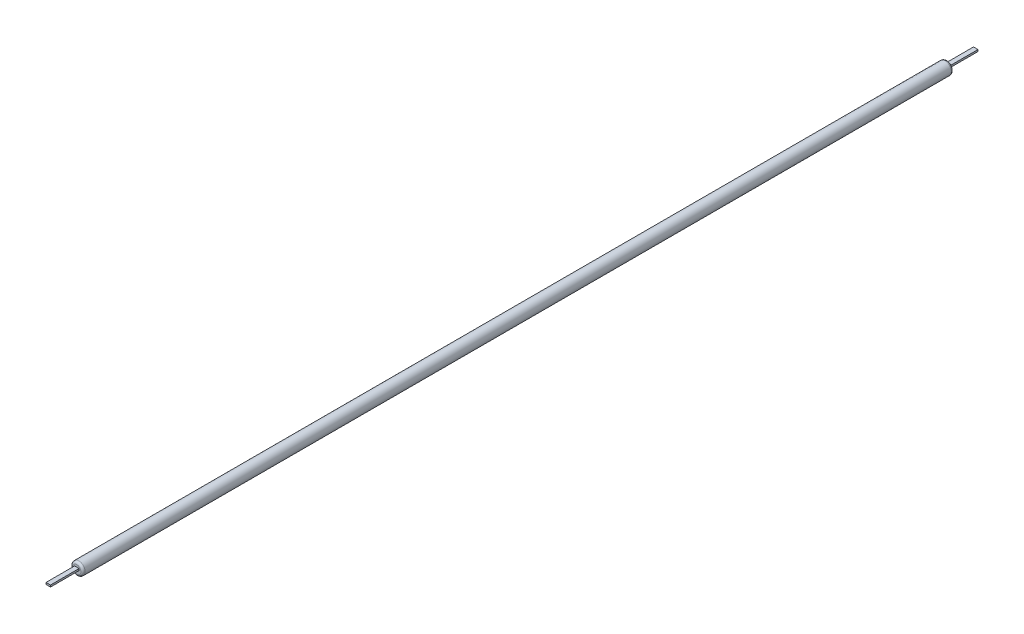
SolidWorks part; units mm, degrees
material "Plastique personnalisé"
ref_plane "Plan de face" through (0, 0, 0) normal (0, 0, 1) x (1, 0, 0)
ref_plane "Plan de dessus" through (0, 0, 0) normal (0, 1, 0) x (1, 0, 0)
ref_plane "Plan de droite" through (0, 0, 0) normal (1, 0, 0) x (0, 0, -1)
sketch "Esquisse1" plane through (0, 0, 0) normal (0, 0, 1) x (1, 0, 0)
  circle A0 centre (0, 0) radius 0.875
extrude "Boss.-Extru.1" add sketch "Esquisse1" along normal blind 122
sketch "Esquisse2" plane through (0, 0, 0) normal (0, 1, 0) x (1, 0, 0)
  line L0 (-0.875, -122) -> (0.875, -122) construction
  line L1 (-0.3149, -4) -> (0.3149, -4)
  line L2 (-0.3149, -4) -> (-0.3149, 4)
  line L3 (-0.3149, 4) -> (0.3149, 4)
  line L4 (0.3149, -4) -> (0.3149, 4)
  line L5 (-0.3149, -4) -> (0.3149, 4) construction
  line L6 (-0.3149, 4) -> (0.3149, -4) construction
  line L7 (-0.3149, -118) -> (0.3149, -118)
  line L8 (-0.3149, -118) -> (-0.3149, -126)
  line L9 (-0.3149, -126) -> (0.3149, -126)
  line L10 (0.3149, -118) -> (0.3149, -126)
  line L11 (-0.3149, -118) -> (0.3149, -126) construction
  line L12 (-0.3149, -126) -> (0.3149, -118) construction
  point P0 (0, 0)
  point P6 (0, -122)
  dimension "D1" = 8
  dimension "D2" = 8
extrude "Boss.-Extru.2" add sketch "Esquisse2" along normal blind 0.25
fillet "Congé1" radius 0.3 2 edges at (0.875, 0, 0) (0.875, 0, 122)
sketch "Esquisse3" plane through (0, 0, 0) normal (0, -1, 0) x (1, 0, 0)
  text T0 "+" font "Century Gothic" height 0.5
extrude "Enlèv. mat.-Extru.1" cut sketch "Esquisse3" against normal blind 0.06
sketch "Esquisse4" plane through (0, 0, 0) normal (0, 1, 0) x (1, 0, 0)
  line L1 (-0.875, -0.3) -> (0.875, -0.3)
  line L2 (-0.875, -0.3) -> (-0.875, -121.7)
  line L3 (-0.875, -121.7) -> (0.875, -121.7)
  line L4 (0.875, -0.3) -> (0.875, -121.7)
